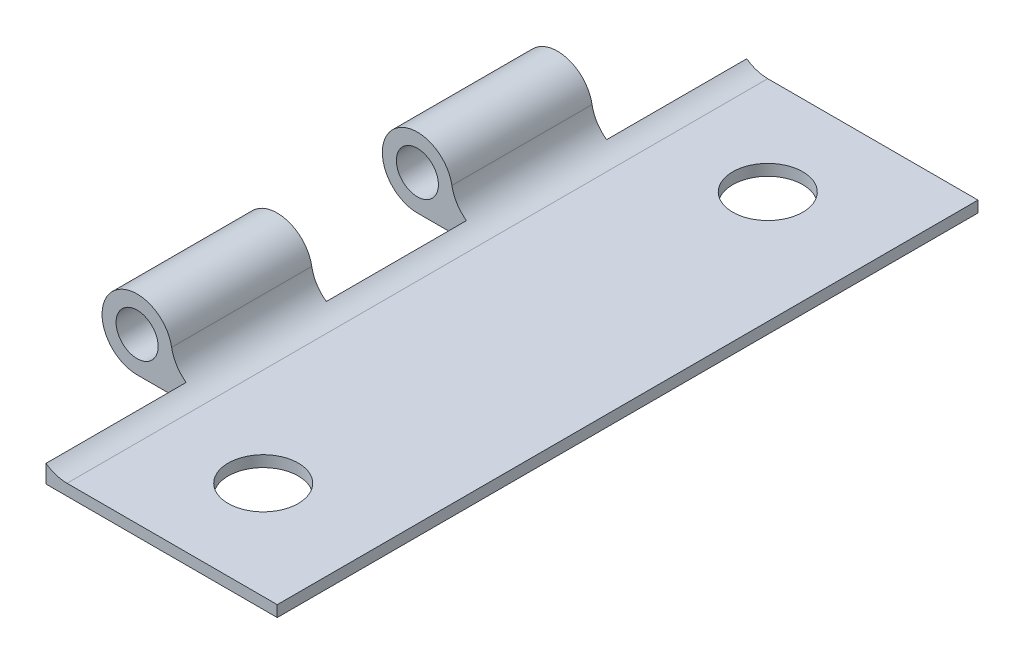
SolidWorks part; units mm, degrees
material "Aço cromo inoxidável"
ref_plane "Plano frontal" through (0, 0, 0) normal (0, 0, 1) x (1, 0, 0)
ref_plane "Plano superior" through (0, 0, 0) normal (0, 1, 0) x (1, 0, 0)
ref_plane "Plano direito" through (0, 0, 0) normal (1, 0, 0) x (0, 0, -1)
sketch "Esboço1" plane through (0, 0, 0) normal (0, 0, 1) x (1, 0, 0)
  line L0 (0, 0) -> (-20, 0)
  line L2 (-15, 0.8) -> (0, 0.8)
  line L3 (0, 0.8) -> (0, 0)
  arc A0 (-20, 0) -> (-18.2893, 4.323) centre (-20, 2.5) cw
  arc A1 (-18.2893, 4.323) -> (-17.5375, 2.9315) centre (-20, 2.5) cw
  arc A2 (-17.5375, 2.9315) -> (-15, 0.8) centre (-15, 3.3762) ccw
  circle A3 centre (-20, 2.5) radius 1.5
  dimension "D4" = 20
  dimension "D5" = 1
  dimension "D2" = 3
  dimension "D1" = 0.8
  dimension "D3" = 5
extrude "Ressalto-extrusão1" add sketch "Esboço1" along normal blind 50
sketch "Esboço2" plane through (0, 0, 0) normal (0, -1, 0) x (1, 0, 0)
  line L0 (-22.5, 50) -> (-22.5, 0) construction
  line L1 (-22.5, 0) -> (-16.5, 0)
  line L2 (-22.5, 0) -> (-22.5, 10)
  line L3 (-22.5, 10) -> (-16.5, 10)
  line L4 (-16.5, 0) -> (-16.5, 10)
  line L5 (0, 50) -> (0, 0) construction
  line L6 (-22.5, 0) -> (-17.5375, 0) construction
  line L7 (-22.5, 20) -> (-22.5, 30)
  line L8 (-22.5, 20) -> (-16.5, 20)
  line L9 (-16.5, 20) -> (-16.5, 30)
  line L10 (-22.5, 30) -> (-16.5, 30)
  line L11 (-22.5, 40) -> (-22.5, 50)
  line L12 (-22.5, 40) -> (-16.5, 40)
  line L13 (-16.5, 40) -> (-16.5, 50)
  line L14 (-22.5, 50) -> (-16.5, 50)
  line L15 (0, 25) -> (-9.0945, 25) construction
  line L16 (0, 50) -> (-15, 50) construction
  circle A0 centre (-8, 43) radius 2.5
  circle A1 centre (-8, 7) radius 2.5
  dimension "D5" = 5
  dimension "D1" = 10
  dimension "D2" = 3
  dimension "D3" = 10
  dimension "D4" = 6
  dimension "D6" = 8
  dimension "D7" = 7
extrude "Corte-extrusão2" cut sketch "Esboço2" against normal through all
